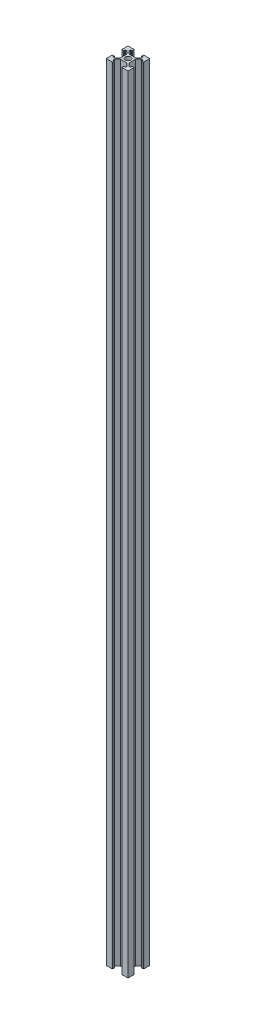
SolidWorks part; units mm, degrees
material "6063-O"
ref_plane "Ön Düzlem" through (0, 0, 0) normal (0, 0, 1) x (1, 0, 0)
ref_plane "Üst Düzlem" through (0, 0, 0) normal (0, 1, 0) x (1, 0, 0)
ref_plane "Sağ Düzlem" through (0, 0, 0) normal (1, 0, 0) x (0, 0, -1)
sketch "Sketch1" plane through (0, 0, 0) normal (0, 1, 0) x (1, 0, 0)
  line L0 (-10, 4.65) -> (-9.8, 4.65)
  line L1 (-9.8, -10) -> (-4.65, -10)
  line L2 (-10, -9.8) -> (-10, -4.65)
  line L3 (-9.8, 10) -> (-4.65, 10)
  line L4 (10, -9.8) -> (10, -4.65)
  line L5 (-10, -10) -> (10, 10) construction
  line L6 (-10, 10) -> (10, -10) construction
  line L7 (-9.8, 4.65) -> (-9.8, 4.4)
  line L8 (-9.6, 4.2) -> (-8.4, 4.2)
  line L9 (-4, 2.8172) -> (-4, -2.8172)
  line L10 (-8.2, 4.4) -> (-8.2, 5.45)
  line L11 (-8, 5.65) -> (-6.8328, 5.65)
  line L12 (-6.6914, 5.5914) -> (-4.0586, 2.9586)
  line L13 (-9.8, -4.65) -> (-10, -4.65)
  line L14 (-6.6914, -5.5914) -> (-4.0586, -2.9586)
  line L15 (-8, -5.65) -> (-6.8328, -5.65)
  line L16 (-8.2, -4.4) -> (-8.2, -5.45)
  line L17 (-9.6, -4.2) -> (-8.4, -4.2)
  line L18 (-9.8, -4.65) -> (-9.8, -4.4)
  line L19 (4.65, 10) -> (4.65, 9.8)
  line L20 (-10, 4.65) -> (-10, 9.8)
  line L21 (4.65, 9.8) -> (4.4, 9.8)
  line L22 (4.2, 9.6) -> (4.2, 8.4)
  line L23 (4.4, 8.2) -> (5.45, 8.2)
  line L24 (5.65, 8) -> (5.65, 6.8328)
  line L25 (5.5914, 6.6914) -> (2.9586, 4.0586)
  line L26 (2.8172, 4) -> (-2.8172, 4)
  line L27 (-5.5914, 6.6914) -> (-2.9586, 4.0586)
  line L28 (-5.65, 8) -> (-5.65, 6.8328)
  line L29 (-4.4, 8.2) -> (-5.45, 8.2)
  line L30 (-4.2, 9.6) -> (-4.2, 8.4)
  line L31 (-4.65, 9.8) -> (-4.4, 9.8)
  line L32 (-4.65, 9.8) -> (-4.65, 10)
  line L33 (10, -4.65) -> (9.8, -4.65)
  line L34 (9.8, -4.65) -> (9.8, -4.4)
  line L35 (9.6, -4.2) -> (8.4, -4.2)
  line L36 (8.2, -4.4) -> (8.2, -5.45)
  line L37 (8, -5.65) -> (6.8328, -5.65)
  line L38 (6.6914, -5.5914) -> (4.0586, -2.9586)
  line L39 (4, -2.8172) -> (4, 2.8172)
  line L40 (6.6914, 5.5914) -> (4.0586, 2.9586)
  line L41 (8, 5.65) -> (6.8328, 5.65)
  line L42 (8.2, 4.4) -> (8.2, 5.45)
  line L43 (9.6, 4.2) -> (8.4, 4.2)
  line L44 (9.8, 4.65) -> (9.8, 4.4)
  line L45 (9.8, 4.65) -> (10, 4.65)
  line L46 (-4.65, -10) -> (-4.65, -9.8)
  line L47 (-4.65, -9.8) -> (-4.4, -9.8)
  line L48 (-4.2, -9.6) -> (-4.2, -8.4)
  line L49 (-4.4, -8.2) -> (-5.45, -8.2)
  line L50 (-5.65, -8) -> (-5.65, -6.8328)
  line L51 (-5.5914, -6.6914) -> (-2.9586, -4.0586)
  line L52 (-2.8172, -4) -> (2.8172, -4)
  line L53 (5.5914, -6.6914) -> (2.9586, -4.0586)
  line L54 (5.65, -8) -> (5.65, -6.8328)
  line L55 (4.4, -8.2) -> (5.45, -8.2)
  line L56 (4.2, -9.6) -> (4.2, -8.4)
  line L57 (4.65, -9.8) -> (4.4, -9.8)
  line L58 (4.65, -9.8) -> (4.65, -10)
  line L59 (4.65, -10) -> (9.8, -10)
  line L60 (10, 4.65) -> (10, 9.8)
  line L61 (4.65, 10) -> (9.8, 10)
  arc A0 (-9.8, 4.4) -> (-9.6, 4.2) centre (-9.6, 4.4) ccw
  arc A1 (-9.8, -4.4) -> (-9.6, -4.2) centre (-9.6, -4.4) cw
  arc A2 (-8.4, 4.2) -> (-8.2, 4.4) centre (-8.4, 4.4) ccw
  arc A3 (-8.2, 5.45) -> (-8, 5.65) centre (-8, 5.45) cw
  arc A4 (-6.6914, 5.5914) -> (-6.8328, 5.65) centre (-6.8328, 5.45) ccw
  arc A5 (-4, 2.8172) -> (-4.0586, 2.9586) centre (-4.2, 2.8172) ccw
  arc A6 (-6.6914, -5.5914) -> (-6.8328, -5.65) centre (-6.8328, -5.45) cw
  arc A7 (-4, -2.8172) -> (-4.0586, -2.9586) centre (-4.2, -2.8172) cw
  arc A8 (-8, -5.65) -> (-8.2, -5.45) centre (-8, -5.45) cw
  arc A9 (-8.2, -4.4) -> (-8.4, -4.2) centre (-8.4, -4.4) ccw
  arc A10 (4.4, 9.8) -> (4.2, 9.6) centre (4.4, 9.6) ccw
  arc A11 (4.2, 8.4) -> (4.4, 8.2) centre (4.4, 8.4) ccw
  arc A12 (5.45, 8.2) -> (5.65, 8) centre (5.45, 8) cw
  arc A13 (5.5914, 6.6914) -> (5.65, 6.8328) centre (5.45, 6.8328) ccw
  arc A14 (2.8172, 4) -> (2.9586, 4.0586) centre (2.8172, 4.2) ccw
  arc A15 (-2.8172, 4) -> (-2.9586, 4.0586) centre (-2.8172, 4.2) cw
  arc A16 (-5.5914, 6.6914) -> (-5.65, 6.8328) centre (-5.45, 6.8328) cw
  arc A17 (-5.65, 8) -> (-5.45, 8.2) centre (-5.45, 8) cw
  arc A18 (-4.4, 8.2) -> (-4.2, 8.4) centre (-4.4, 8.4) ccw
  arc A19 (-4.4, 9.8) -> (-4.2, 9.6) centre (-4.4, 9.6) cw
  arc A20 (9.8, -4.4) -> (9.6, -4.2) centre (9.6, -4.4) ccw
  arc A21 (8.4, -4.2) -> (8.2, -4.4) centre (8.4, -4.4) ccw
  arc A22 (8.2, -5.45) -> (8, -5.65) centre (8, -5.45) cw
  arc A23 (6.6914, -5.5914) -> (6.8328, -5.65) centre (6.8328, -5.45) ccw
  arc A24 (4, -2.8172) -> (4.0586, -2.9586) centre (4.2, -2.8172) ccw
  arc A25 (4, 2.8172) -> (4.0586, 2.9586) centre (4.2, 2.8172) cw
  arc A26 (6.6914, 5.5914) -> (6.8328, 5.65) centre (6.8328, 5.45) cw
  arc A27 (8, 5.65) -> (8.2, 5.45) centre (8, 5.45) cw
  arc A28 (8.2, 4.4) -> (8.4, 4.2) centre (8.4, 4.4) ccw
  arc A29 (9.8, 4.4) -> (9.6, 4.2) centre (9.6, 4.4) cw
  arc A30 (-4.4, -9.8) -> (-4.2, -9.6) centre (-4.4, -9.6) ccw
  arc A31 (-4.2, -8.4) -> (-4.4, -8.2) centre (-4.4, -8.4) ccw
  arc A32 (-5.45, -8.2) -> (-5.65, -8) centre (-5.45, -8) cw
  arc A33 (-5.5914, -6.6914) -> (-5.65, -6.8328) centre (-5.45, -6.8328) ccw
  arc A34 (-2.8172, -4) -> (-2.9586, -4.0586) centre (-2.8172, -4.2) ccw
  arc A35 (2.8172, -4) -> (2.9586, -4.0586) centre (2.8172, -4.2) cw
  arc A36 (5.5914, -6.6914) -> (5.65, -6.8328) centre (5.45, -6.8328) cw
  arc A37 (5.65, -8) -> (5.45, -8.2) centre (5.45, -8) cw
  arc A38 (4.4, -8.2) -> (4.2, -8.4) centre (4.4, -8.4) ccw
  arc A39 (4.4, -9.8) -> (4.2, -9.6) centre (4.4, -9.6) cw
  arc A40 (-9.8, -10) -> (-10, -9.8) centre (-9.8, -9.8) cw
  arc A41 (9.8, -10) -> (10, -9.8) centre (9.8, -9.8) ccw
  arc A42 (10, 9.8) -> (9.8, 10) centre (9.8, 9.8) ccw
  arc A43 (-10, 9.8) -> (-9.8, 10) centre (-9.8, 9.8) cw
  circle A44 centre (0, 0) radius 2.5
  point P0 (0, 0)
  point P12 (-9.8, 4.2)
  point P27 (-9.8, -4.2)
  point P30 (-8.2, 4.2)
  point P33 (-8.2, 5.65)
  point P36 (-6.75, 5.65)
  point P39 (-4, 2.9)
  point P42 (-6.75, -5.65)
  point P45 (-4, -2.9)
  point P48 (-8.2, -5.65)
  point P51 (-8.2, -4.2)
  dimension "D11" = 0.2
  dimension "D13" = 0.2
  dimension "D14" = 5
  dimension "D1" = 20
  dimension "D2" = 20
  dimension "D3" = 5.35
  dimension "D4" = 0.2
  dimension "D5" = 0.45
  dimension "D6" = 1.6
  dimension "D7" = 4.2
  dimension "D8" = 1.45
  dimension "D9" = 1.45
  dimension "D10" = 135
  dimension "D12" = 4
extrude "Boss-Extrude1" add sketch "Sketch1" along normal blind 720
